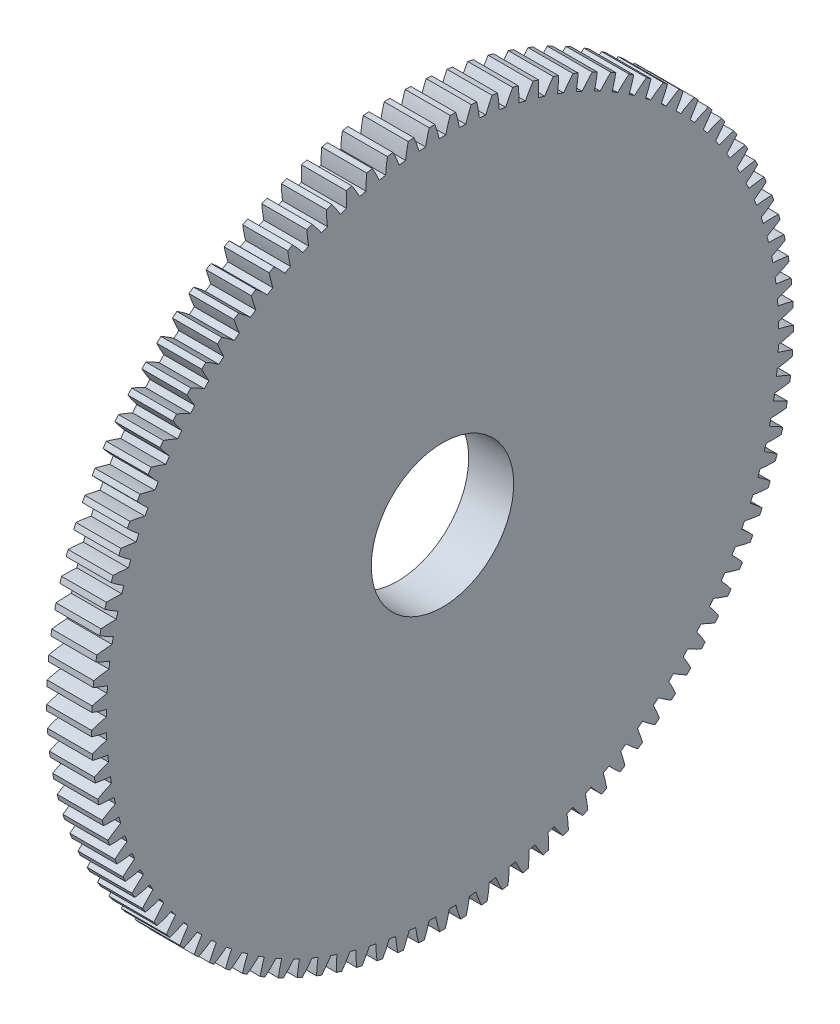
SolidWorks part; units mm, degrees
ref_plane "Plane1" through (0, 0, 0) normal (0, 0, 1) x (1, 0, 0)
ref_plane "Plane2" through (0, 0, 0) normal (0, 1, 0) x (1, 0, 0)
ref_plane "Plane3" through (0, 0, 0) normal (1, 0, 0) x (0, 0, -1)
sketch "HoldingSke" plane through (0, 0, 0) normal (0, 1, 0) x (1, 0, 0)
  line L0 (0, 0) -> (-0.1479, -0.552)
  line L1 (-15, 0) -> (100, 0) construction
  line L2 (0, 0) -> (-2.1039, 2.3779)
  line L3 (0, 0) -> (-11.863, 4.5341)
  line L4 (0, 0) -> (-2.2352, 8.3417)
  line L5 (0, 0) -> (-46.8476, -17.4728)
  line L6 (0, 0) -> (-9.9476, -6.7116)
  line L7 (-2.1039, 2.3779) -> (8.6586, 51.2059)
  line L8 (-76.2, 54.61) -> (-72.9, 54.61)
  line L9 (-67.7845, 28.3722) -> (-49.3413, 33.142)
  line L10 (-76.2, 71.12) -> (104.1128, 71.12)
  line L11 (0, 0) -> (-12, 0)
  line L12 (-76.2, 101.6) -> (-76.147, 101.6)
  line L13 (24.9733, 27.94) -> (52.9518, 28.4284)
  line L14 (24.9733, 27.94) -> (24.9743, 27.94)
  line L15 (24.9733, 27.94) -> (100.4006, 29.5858)
  line L16 (-63.627, -1.75) -> (-12.827, -1.75)
  circle A0 centre (0, 0) radius 19
  circle A1 centre (0, 0) radius 37.5
  circle A2 centre (0, 0) radius 37.5
  circle A3 centre (0, 0) radius 19
  dimension "MHD" = 75
  dimension "Hub_dia" = 75
  dimension "Bore" = 38
  dimension "MBD" = 38
  dimension "Num_teeth" = 105
  dimension "Pitch" = 0.5714
  dimension "Overall_len" = 50
  dimension "Show_teeth" = 105
  dimension "Thickness" = 12
  dimension "OAL" = 50.0001
  dimension "T_dim" = 3.3
  dimension "Ap" = 14.5
  dimension "H" = 19.05
  dimension "Pitch_radius" = 180.3128
  dimension "Width" = 12
  dimension "Backlash" = 0.053
  dimension "Addendum_fac" = 1
  dimension "Dedendum_fac" = 1.25
  dimension "Clearance_fac" = 0.25
  dimension "Dedendum_add" = 0.001
  dimension "Module" = 1.75
sketch "BasProSke" plane through (0, 0, 0) normal (0, 1, 0) x (1, 0, 0)
  line L0 (-10, 0) -> (60, 0) construction
  line L1 (0, 0) -> (0, 93.625)
  line L2 (0, 0) -> (12, 0)
  line L3 (12, 0) -> (12, 93.625)
  line L4 (12, 93.625) -> (0, 93.625)
  dimension "Thickness" = 12
  dimension "Diameter" = 187.25
revolve "Base-Revolve" add sketch "BasProSke" angle 360 about L0
sketch "TooCutSke" plane through (0, 0, 0) normal (1, 0, 0) x (0, 0, -1)
  line L1 (0, 0) -> (0, 107) construction
  line L2 (0, 0) -> (-1.4671, 91.8633) construction
  line L3 (0, 0) -> (-5.4964, 183.6499) construction
  line L4 (-1.4671, 91.8633) -> (-2.7482, 91.8249) construction
  arc A0 (0.8699, 89.6823) -> (-0.8699, 89.6823) centre (0, 0) ccw
  arc A1 (2.0585, 93.6278) -> (-2.0585, 93.6278) centre (0, 0) ccw
  circle A2 centre (0, 0) radius 91.875 construction
  circle A3 centre (0, 0) radius 88.9486 construction
  arc A4 (-0.8699, 89.6823) -> (-2.0585, 93.6278) centre (-36.5968, 81.0711) ccw
  arc A5 (2.0585, 93.6278) -> (0.8699, 89.6823) centre (36.5968, 81.0711) ccw
  dimension "Root_dia" = 179.373
  dimension "Overcut_dia" = 187.3008
  dimension "Pitch_dia" = 183.75
  dimension "Base_dia" = 177.8971
  dimension "Flank_rad" = 36.75
  dimension "Half_ang" = 1.714
  dimension "Half_CT" = 1.2816
extrude "ToothCut" cut sketch "TooCutSke" along normal through all
fillet "Breaks" [suppressed] radius 0.035
fillet "RootFillets" [suppressed] radius 0.4385
pattern_circular "TeethCuts" count 105 every 3.429 about axis through (-10, 0, 0) along (1, 0, 0) of "ToothCut", "RootFillets", "Breaks"
sketch "HubNeaOneSke" plane through (0, 0, 0) normal (-1, 0, 0) x (0, 0, 1)
  circle A0 centre (0, 0) radius 37.5
  dimension "Diameter" = 75
extrude "HubNearOne" [suppressed] add sketch "HubNeaOneSke" along normal blind 38.0001
sketch "HubNeaBotSke" plane through (0, 0, 0) normal (-1, 0, 0) x (0, 0, 1)
  circle A0 centre (0, 0) radius 37.5
  dimension "Diameter" = 75
extrude "HubNearBoth" [suppressed] add sketch "HubNeaBotSke" along normal blind 19
ref_plane "FarPln" through (12, 0, 0) normal (1, 0, 0) x (0, 0, -1)
sketch "HubFarSke" plane through (12, 0, 0) normal (1, 0, 0) x (0, 0, -1)
  circle A0 centre (0, 0) radius 37.5
  dimension "Diameter" = 75
extrude "HubFar" [suppressed] add sketch "HubFarSke" along normal blind 19
sketch "BorSke" plane through (0, 0, 0) normal (1, 0, 0) x (0, 0, -1)
  circle A0 centre (0, 0) radius 19
  dimension "Diameter" = 38
extrude "Bore" cut sketch "BorSke" along normal mid plane 100.0001
sketch "KeySke" plane through (0, 0, 0) normal (1, 0, 0) x (0, 0, -1)
  line L0 (-6, 0) -> (-6, 22.3)
  line L1 (-6, 22.3) -> (6, 22.3)
  line L2 (6, 22.3) -> (6, 0)
  line L3 (0, 0) -> (0, 34) construction
  line L4 (-6, 0) -> (6, 0)
  dimension "Width" = 12
  dimension "Offset" = 22.3
extrude "Keyway" [suppressed] cut sketch "KeySke" along normal mid plane 100.0001
pattern_circular "Keyway2" [suppressed] count 2 every 90 about axis through (-10, 0, 0) along (1, 0, 0)
equation "' \"Module@HoldingSke\" = 6.35"
equation "' \"Num_teeth@HoldingSke\" = 12"
equation "' \"Ap@HoldingSke\" =  20"
equation "' \"Ap@HoldingSke\" = 20"
equation "' \"Width@HoldingSke\" = 0.5 * 25.4"
equation "' \"Hub_dia@HoldingSke\"= 1 * 25.4"
equation "' \"Hub_dia@HoldingSke\" = 1 * 25.4"
equation "' \"Overall_len@HoldingSke\" = 1.0 * 25.4"
equation "' \"Bore@HoldingSke\" = 0.75 * 25.4"
equation "' \"T_dim@HoldingSke\" = 0.1 * 25.4"
equation "' \"Width@KeySke\" = 0.25 * 25.4"
equation "' \"Show_teeth@HoldingSke\" = 13"
equation "' \"Backlash@HoldingSke\" = 0.009 * 25.4"
equation "' \"Addendum_fac@HoldingSke\" = 1.0"
equation "' \"Dedendum_fac@HoldingSke\" = 1.25"
equation "' \"Dedendum_add@HoldingSke\" = 0.00005 * 25.4"
equation "' \"Clearance_fac@HoldingSke\" = 0.25"
equation "\"Pitch@HoldingSke\" = 1 / \"Module@HoldingSke\""
equation "\"Overcut_dia@TooCutSke\" = (\"Num_teeth@HoldingSke\" + 2 * \"Addendum_fac@HoldingSke\") / \"Pitch@HoldingSke\" + 0.002 * 25.4"
equation "\"Pitch_dia@TooCutSke\" = \"Num_teeth@HoldingSke\" / \"Pitch@HoldingSke\""
equation "\"Base_dia@TooCutSke\" = \"Num_teeth@HoldingSke\" / \"Pitch@HoldingSke\" * cos((\"Ap@HoldingSke\"  * 3.14159265 / 180))"
equation "\"Root_dia@TooCutSke\" = (\"Num_teeth@HoldingSke\" + 2) / \"Pitch@HoldingSke\" - 2 * (\"Addendum_fac@HoldingSke\" + \"Dedendum_fac@HoldingSke\") / \"Pitch@HoldingSke\" - \"Dedendum_add@HoldingSke\" * 2"
equation "\"Half_ang@TooCutSke\" = 180 / \"Num_teeth@HoldingSke\""
equation "\"Half_CT@TooCutSke\" = \"Num_teeth@HoldingSke\" / \"Pitch@HoldingSke\" * sin((3.14159265 / 2 / \"Num_teeth@HoldingSke\")) / 2 - 7 * \"Backlash@HoldingSke\" / 4"
equation "\"Flank_rad@TooCutSke\" = \"Num_teeth@HoldingSke\" / \"Pitch@HoldingSke\" / 5"
equation "\"Radius@RootFillets\" = \"Clearance_fac@HoldingSke\" / \"Pitch@HoldingSke\" + \"Dedendum_add@HoldingSke\""
equation "\"Break_rad@Breaks\" = 0.02 / \"Pitch@HoldingSke\""
equation "\"Thickness@HoldingSke\" = \"Width@HoldingSke\""
equation "\"OAL@HoldingSke\" = \"Thickness@HoldingSke\""
equation "\"MHD@HoldingSke\" = (\"Num_teeth@HoldingSke\" + 2) / \"Pitch@HoldingSke\" - 2 * (\"Addendum_fac@HoldingSke\" + \"Dedendum_fac@HoldingSke\")  / \"Pitch@HoldingSke\" - \"Dedendum_add@HoldingSke\" * 2"
equation "\"MBD@HoldingSke\" = (\"Num_teeth@HoldingSke\" + 2) / \"Pitch@HoldingSke\" - 2 * (\"Addendum_fac@HoldingSke\" + \"Dedendum_fac@HoldingSke\")  / \"Pitch@HoldingSke\" - \"Dedendum_add@HoldingSke\" * 2 - 0.002 * 25.4"
equation "\"MHD@HoldingSke\" = ((sgn( \"MHD@HoldingSke\" - \"Hub_dia@HoldingSke\" )-1)*( \"MHD@HoldingSke\" - \"Hub_dia@HoldingSke\" ))/-2+ \"Hub_dia@HoldingSke\""
equation "\"MBD@HoldingSke\" = ((sgn( \"MBD@HoldingSke\" - \"Bore@HoldingSke\" )-1)*( \"MBD@HoldingSke\" - \"Bore@HoldingSke\" ))/-2+ \"Bore@HoldingSke\""
equation "\"OAL@HoldingSke\" = ((sgn( \"OAL@HoldingSke\" - \"Overall_len@HoldingSke\" )+1)*( \"OAL@HoldingSke\" - \"Overall_len@HoldingSke\" ))/2 + \"Overall_len@HoldingSke\" + 0.000002 * 25.4"
equation "\"Num_teeth@TeethCuts\" = int( \"Show_teeth@HoldingSke\" ) + 1"
equation "\"Num_teeth@TeethCuts\" = ((sgn( \"Num_teeth@TeethCuts\" - \"Num_teeth@HoldingSke\" )-1)*( \"Num_teeth@TeethCuts\" - \"Num_teeth@HoldingSke\" ))/-2+ \"Num_teeth@HoldingSke\""
equation "\"Num_teeth@TeethCuts\" = ((sgn( \"Num_teeth@TeethCuts\" - 2.0)+1)*( \"Num_teeth@TeethCuts\" - 2.0))/2 +2.0"
equation "\"Angle@TeethCuts\" = 360.0 / \"Num_teeth@HoldingSke\""
equation "\"Diameter@BasProSke\" = (\"Num_teeth@HoldingSke\" + 2 * \"Addendum_fac@HoldingSke\") / \"Pitch@HoldingSke\""
equation "\"Thickness@BasProSke\"  = \"Thickness@HoldingSke\""
equation "' \"Fillet_rad@BasProSke\" =  \"Thickness@HoldingSke\" * 0.05"
equation "' \"Fillet_rad@BasProSke\" = \"Thickness@HoldingSke\" * 0.05"
equation "\"MHD@HoldingSke\" = ((sgn( \"MHD@HoldingSke\" - \"Root_dia@TooCutSke\" )-1)*( \"MHD@HoldingSke\" - \"Root_dia@TooCutSke\" ))/-2+ \"Root_dia@TooCutSke\""
equation "\"Diameter@HubNeaOneSke\" = \"MHD@HoldingSke\""
equation "\"Length@HubNearOne\" = \"OAL@HoldingSke\" - \"Thickness@BasProSke\""
equation "\"Diameter@HubNeaBotSke\" = \"MHD@HoldingSke\""
equation "\"Length@HubNearBoth\" = ( \"OAL@HoldingSke\" - \"Thickness@BasProSke\" ) / 2.0"
equation "\"Thickness@FarPln\" = \"Thickness@BasProSke\""
equation "\"Diameter@HubFarSke\" = \"MHD@HoldingSke\""
equation "\"Length@HubFar\" = ( \"OAL@HoldingSke\" - \"Thickness@BasProSke\" ) / 2.0"
equation "\"Diameter@BorSke\" = \"MBD@HoldingSke\""
equation "\"D1@Bore\" = \"OAL@HoldingSke\" * 2.0"
equation "\"D1@Keyway\" = \"OAL@HoldingSke\" * 2.0"
equation "\"Offset@KeySke\" = \"T_dim@HoldingSke\" + \"MBD@HoldingSke\" / 2.0"
